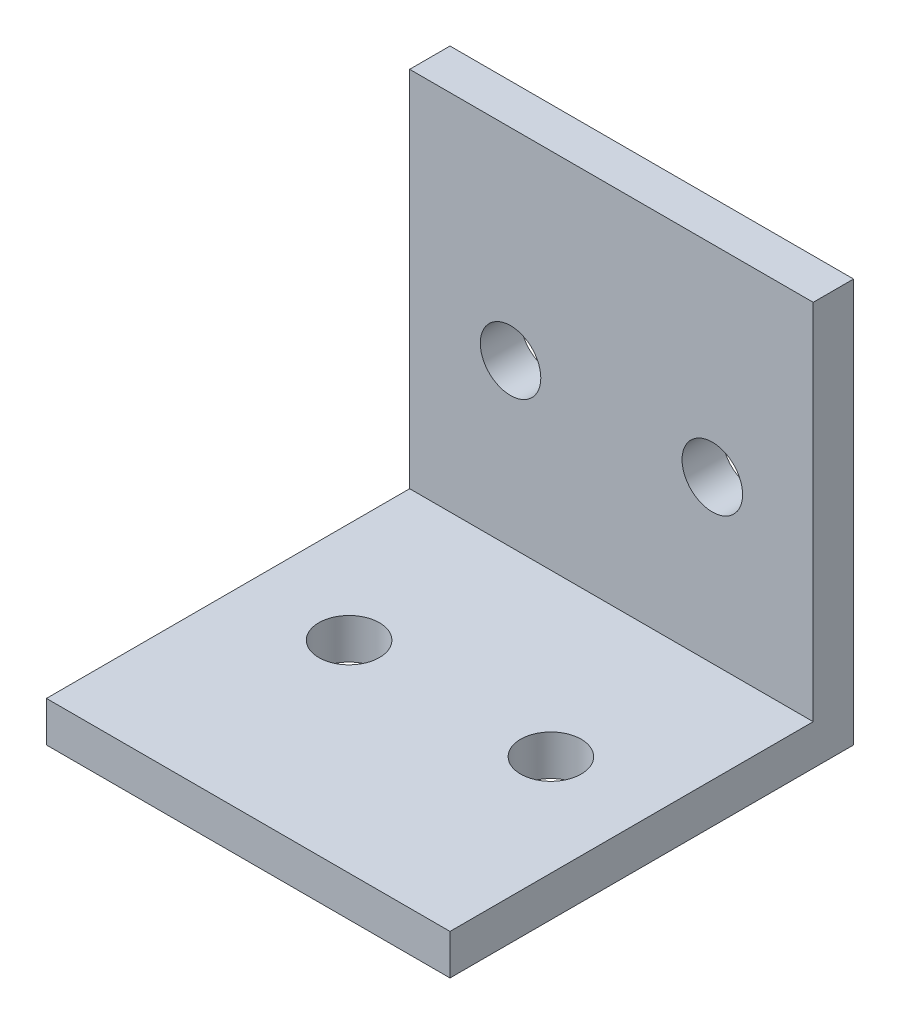
SolidWorks part; units mm, degrees
ref_plane "前视基准面" through (0, 0, 0) normal (0, 0, 1) x (1, 0, 0)
ref_plane "上视基准面" through (0, 0, 0) normal (0, 1, 0) x (1, 0, 0)
ref_plane "右视基准面" through (0, 0, 0) normal (1, 0, 0) x (0, 0, -1)
sketch "草图1" plane through (0, 0, 0) normal (0, 0, 1) x (1, 0, 0)
  line L1 (-10, 10) -> (10, 10)
  line L2 (-10, 10) -> (-10, -10)
  line L3 (-10, -10) -> (10, -10)
  line L4 (10, 10) -> (10, -10)
  line L5 (-10, 10) -> (10, -10) construction
  line L6 (-10, -10) -> (10, 10) construction
  point P0 (0, 0)
  dimension "D1" = 20
  dimension "D2" = 20
extrude "凸台-拉伸1" add sketch "草图1" along normal blind 2
sketch "草图2" plane through (0, 0, 2) normal (0, 0, 1) x (1, 0, 0)
  line L0 (10, -10) -> (10, 10) construction
  line L1 (-10, -10) -> (10, -10)
  line L2 (-10, -10) -> (-10, -8)
  line L3 (-10, -8) -> (10, -8)
  line L4 (10, -10) -> (10, -8)
  dimension "D1" = 2
extrude "凸台-拉伸2" add sketch "草图2" along normal blind 18
sketch "草图4" plane through (0, -10, 0) normal (0, -1, 0) x (1, 0, 0)
  line L0 (-10, 20) -> (-10, 0) construction
  line L1 (10, 20) -> (10, 0) construction
  line L2 (-10, 20) -> (10, 20) construction
  circle A0 centre (-5, 10) radius 1.5
  circle A1 centre (5, 10) radius 1.5
  dimension "D1" = 3
  dimension "D2" = 3
  dimension "D3" = 5
  dimension "D4" = 5
  dimension "D5" = 10
extrude "切除-拉伸1" cut sketch "草图4" against normal blind 18
sketch "草图6" plane through (0, 0, 0) normal (0, 0, -1) x (-1, 0, 0)
  line L0 (-10, -10) -> (-10, 10) construction
  line L1 (10, 10) -> (10, -10) construction
  line L2 (10, -10) -> (-10, -10) construction
  circle A0 centre (5, 0) radius 1.5
  circle A1 centre (-5, 0) radius 1.5
  dimension "D1" = 3
  dimension "D2" = 3
  dimension "D3" = 5
  dimension "D4" = 5
  dimension "D5" = 10
extrude "切除-拉伸2" cut sketch "草图6" against normal blind 18
